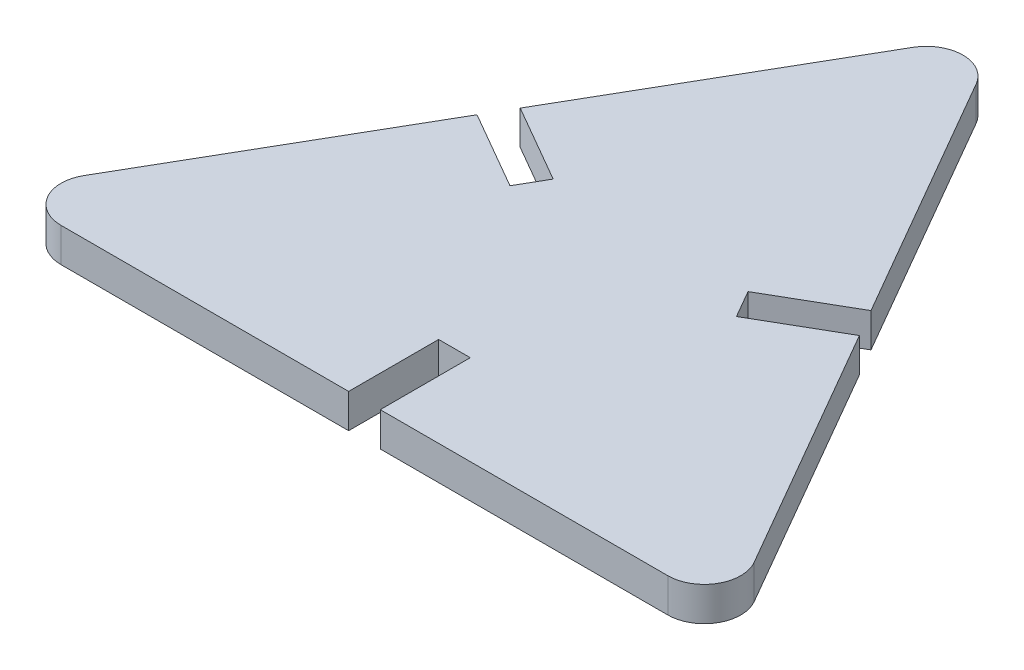
SolidWorks part; units mm, degrees
ref_plane "Ebene vorne" through (0, 0, 0) normal (0, 0, 1) x (1, 0, 0)
ref_plane "Ebene oben" through (0, 0, 0) normal (0, 1, 0) x (1, 0, 0)
ref_plane "Ebene rechts" through (0, 0, 0) normal (1, 0, 0) x (0, 0, -1)
sketch "Sketch1" plane through (0, 0, 0) normal (0, 1, 0) x (1, 0, 0)
  line L0 (1.3, -17.4) -> (24.9415, -17.4)
  line L1 (-2.5981, 30.3) -> (-14.4188, 9.8258)
  line L2 (-24.9415, -17.4) -> (-1.3, -17.4)
  line L3 (27.5396, -12.9) -> (15.7188, 7.5742)
  line L4 (-14.4188, 9.8258) -> (-8.0103, 6.1258)
  line L5 (-1.3, -17.4) -> (-1.3, -10)
  line L6 (-1.3, -10) -> (1.3, -10)
  line L7 (1.3, -17.4) -> (1.3, -10)
  line L8 (-15.7188, 7.5742) -> (-9.3103, 3.8742)
  line L9 (-8.0103, 6.1258) -> (-9.3103, 3.8742)
  line L10 (15.7188, 7.5742) -> (9.3103, 3.8742)
  line L11 (14.4188, 9.8258) -> (8.0103, 6.1258)
  line L12 (9.3103, 3.8742) -> (8.0103, 6.1258)
  line L13 (-15.7188, 7.5742) -> (-27.5396, -12.9)
  line L14 (14.4188, 9.8258) -> (2.5981, 30.3)
  circle A0 centre (0, 0) radius 17.4 construction
  arc A1 (24.9415, -17.4) -> (27.5396, -12.9) centre (24.9415, -14.4) ccw
  arc A2 (2.5981, 30.3) -> (-2.5981, 30.3) centre (0, 28.8) ccw
  arc A3 (-24.9415, -17.4) -> (-27.5396, -12.9) centre (-24.9415, -14.4) cw
  point P21 (0, 0)
extrude "Boss-Extrude1" add sketch "Sketch1" along normal blind 2.8
equation "\"D2@Sketch1\"=(\"Slot Width\")/2"
equation "\"D1@Sketch1\"=(\"D5@Sketch1\"+\"Slot Width\")/2"
equation "\"D5@Sketch1\"=20.0-(\"Slot Width\")"
